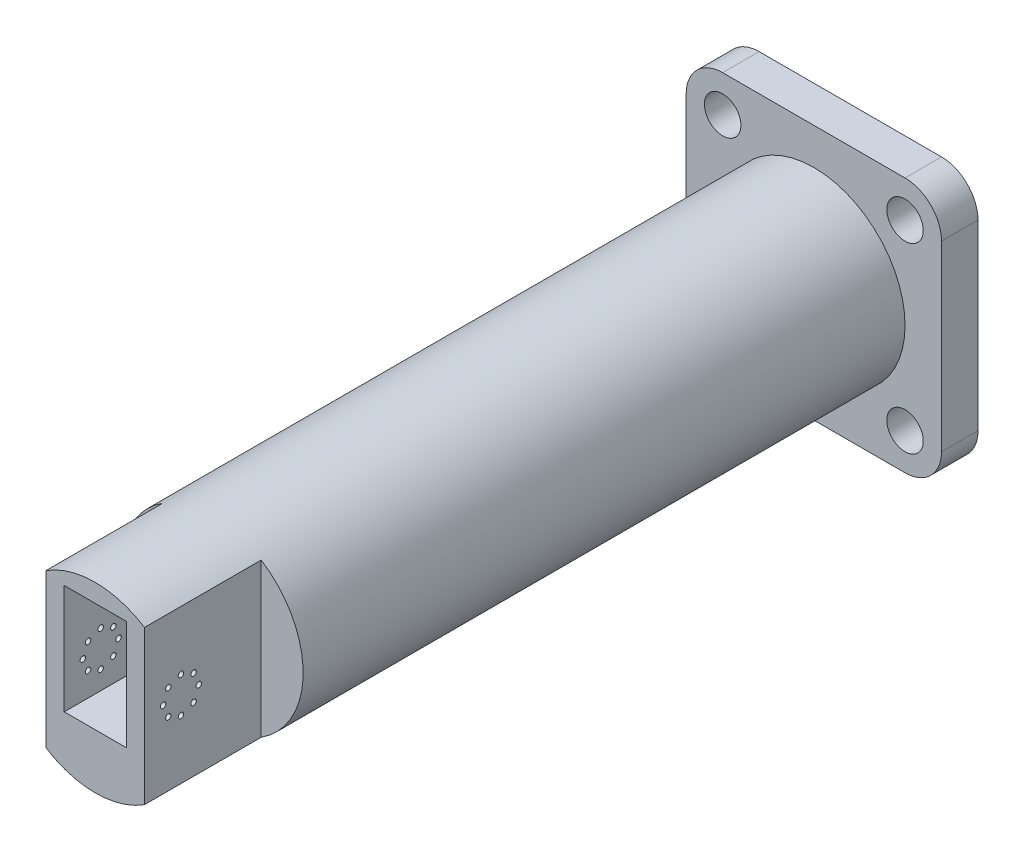
SolidWorks part; units mm, degrees
ref_plane "Alzado" through (0, 0, 0) normal (0, 0, 1) x (1, 0, 0)
ref_plane "Planta" through (0, 0, 0) normal (0, 1, 0) x (1, 0, 0)
ref_plane "Vista lateral" through (0, 0, 0) normal (1, 0, 0) x (0, 0, -1)
sketch "Croquis1" plane through (0, 0, 0) normal (0, 0, 1) x (1, 0, 0)
  line L1 (-17, -30) -> (17, -30)
  line L2 (-17, -30) -> (-17, 30)
  line L3 (-17, 30) -> (17, 30)
  line L4 (17, -30) -> (17, 30)
  line L5 (-17, -30) -> (17, 30) construction
  line L6 (-17, 30) -> (17, -30) construction
  line L7 (-21, -34) -> (21, -34)
  line L8 (-21, -34) -> (-21, 34)
  line L9 (-21, 34) -> (21, 34)
  line L10 (21, -34) -> (21, 34)
  line L11 (-21, -34) -> (21, 34) construction
  line L12 (-21, 34) -> (21, -34) construction
  point P0 (0, 0)
  point P6 (0, 0)
extrude "Saliente-Extruir1" add sketch "Croquis1" along normal blind 60
sketch "Croquis2" plane through (-17, 0, 0) normal (1, 0, 0) x (0, 0, -1)
  circle A3 centre (-49.779, -10) radius 1.5
  circle A4 centre (-46.9148, -3.0852) radius 1.5
  circle A5 centre (-40, -0.221) radius 1.5
  circle A6 centre (-33.0852, -3.0852) radius 1.5
  circle A7 centre (-30.221, -10) radius 1.5
  circle A8 centre (-33.0852, -16.9148) radius 1.5
  circle A9 centre (-40, -19.779) radius 1.5
  circle A10 centre (-46.9148, -16.9148) radius 1.5
  point P29 (-40, -10)
  dimension "D1" = 8
extrude "Cortar-Extruir1" cut sketch "Croquis2" against normal through all both and the other way through all
sketch "Croquis3" plane through (0, 0, 0) normal (0, 0, -1) x (-1, 0, 0)
  line L1 (-21, -34) -> (21, -34)
  line L2 (-21, -34) -> (-21, 34)
  line L3 (-21, 34) -> (21, 34)
  line L4 (21, -34) -> (21, 34)
extrude "Saliente-Extruir2" add sketch "Croquis3" along normal blind 4
sketch "Croquis4" plane through (21, 0, 0) normal (1, 0, 0) x (0, 0, -1)
  line L0 (-49.779, -10) -> (4, -10)
  line L1 (4, 34) -> (4, -34) construction
  line L2 (4, -34) -> (4, -54)
  line L3 (4, -54) -> (-60, -54)
  line L4 (-60, -54) -> (-60, -34)
  line L5 (-60, -34) -> (4, -34)
  line M10 (-60, -34) -> (4, -34)
extrude "Saliente-Extruir3" add sketch "Croquis4" against normal up to surface (42 mm away) contours L4 L3 L2 M10 up to face at (-21, -16.9148, 45.4148)
sketch "Croquis5" plane through (0, 0, -4) normal (0, 0, -1) x (-1, 0, 0)
  line L4 (-21, -54) -> (21, -54)
  line L5 (-21, -54) -> (-21, 34)
  line L7 (21, -54) -> (21, 34)
  line L8 (-21, -54) -> (21, 34) construction
  line L9 (-21, 34) -> (21, -54) construction
  arc A0 (-21, -54) -> (21, -54) centre (0, -10) ccw
  arc A1 (21, 34) -> (-21, 34) centre (0, -10) ccw
  point P4 (0, -10)
  line M7 (-21, -54) -> (21, -54)
  line M9 (21, 34) -> (-21, 34)
extrude "Saliente-Extruir4" add sketch "Croquis5" against normal up to surface (64 mm away) contours A1 M9 | A0 M7 up to face at (0, -10, 60)
sketch "Croquis6" plane through (0, 0, -4) normal (0, 0, -1) x (-1, 0, 0)
  line L1 (-21, 34) -> (21, 34)
  line L3 (-21, -55.3762) -> (-21, -54)
  line L5 (21, -55.3762) -> (21, -54)
  line L6 (-21, -55.3762) -> (21, 35.3762) construction
  line L7 (-21, 35.3762) -> (21, -55.3762) construction
  line L8 (-21, -54) -> (21, -54)
  line L9 (-21, 34) -> (-21, 35.3762)
  line L10 (21, 34) -> (21, 35.3762)
  arc A3 (-21, -55.3762) -> (21, -55.3762) centre (0, -10) ccw
  arc A4 (21, 35.3762) -> (-21, 35.3762) centre (0, -10) ccw
extrude "Saliente-Extruir6" add sketch "Croquis6" against normal up to surface (64 mm away) up to face at (0, -10, 60)
sketch "Croquis8" plane through (0, 0, -4) normal (0, 0, -1) x (-1, 0, 0)
  circle A0 centre (0, -10) radius 50
extrude "Saliente-Extruir7" add sketch "Croquis8" along normal blind 350
sketch "Croquis10" plane through (0, 0, 0) normal (0, 0, 1) x (1, 0, 0)
  line L2 (-21, 35.3762) -> (-21, -55.3762)
  line L3 (20.8781, -55.3762) -> (21, -55.3762)
  line L4 (21, 35.3762) -> (21, -55.3762)
  line L10 (27, -52.0833) -> (27, 32.0833)
  line L12 (-27, -52.0833) -> (-27, 32.0833)
  arc A0 (27, 32.0833) -> (21, 35.3762) centre (0, -10) ccw
  arc A1 (-27, -52.0833) -> (-21, -55.3762) centre (0, -10) ccw
  arc A2 (21, -55.3762) -> (27, -52.0833) centre (0, -10) ccw
  arc A3 (-21, 35.3762) -> (-27, 32.0833) centre (0, -10) ccw
  point P15 (0, 0)
extrude "Saliente-Extruir8" add sketch "Croquis10" along normal up to surface and the other way up to surface contours L2 A3 L12 A1 | L4 A2 L10 A0
sketch "Croquis11" plane through (-17, 0, 0) normal (1, 0, 0) x (0, 0, -1)
  circle A0 centre (-49.779, -10) radius 1.5
  circle A1 centre (-46.9148, -3.0852) radius 1.5
  circle A2 centre (-40, -0.221) radius 1.5
  circle A3 centre (-33.0852, -3.0852) radius 1.5
  circle A4 centre (-30.221, -10) radius 1.5
  circle A5 centre (-33.0852, -16.9148) radius 1.5
  circle A6 centre (-40, -19.779) radius 1.5
  circle A8 centre (-46.9148, -16.9148) radius 1.5
extrude "Cortar-Extruir2" cut sketch "Croquis11" against normal through all both and the other way through all
sketch "Croquis12" [suppressed] plane through (27, 0, 0) normal (1, 0, 0) x (0, 0, -1)
  circle A0 centre (-33.0852, -3.0852) radius 3
  circle A1 centre (-40, -0.221) radius 3
  circle A2 centre (-46.9148, -3.0852) radius 3
  circle A3 centre (-49.779, -10) radius 3
  circle A4 centre (-46.9148, -16.9148) radius 3
  circle A5 centre (-40, -19.779) radius 3
  circle A6 centre (-33.0852, -16.9148) radius 3
  circle A7 centre (-30.221, -10) radius 3
sketch "Croquis13" plane through (0, 0, -354) normal (0, 0, -1) x (-1, 0, 0)
  line L1 (-50, -80) -> (50, -80)
  line L2 (-70, -60) -> (-70, 40)
  line L3 (-50, 60) -> (50, 60)
  line L4 (70, -60) -> (70, 40)
  line L5 (-70, -80) -> (70, 60) construction
  line L6 (-70, 60) -> (70, -80) construction
  arc A0 (-50, 60) -> (-70, 40) centre (-50, 40) ccw
  arc A1 (70, 40) -> (50, 60) centre (50, 40) ccw
  arc A2 (50, -80) -> (70, -60) centre (50, -60) ccw
  arc A3 (-70, -60) -> (-50, -80) centre (-50, -60) ccw
  circle A4 centre (-50, 40) radius 10
  circle A5 centre (-50, -60) radius 10
  circle A6 centre (50, 40) radius 10
  circle A7 centre (50, -60) radius 10
  circle A8 centre (0, -10) radius 50
  point P0 (0, -10)
  point P17 (0, -10)
  dimension "D1" = 4
extrude "Saliente-Extruir9" add sketch "Croquis13" against normal blind 20
